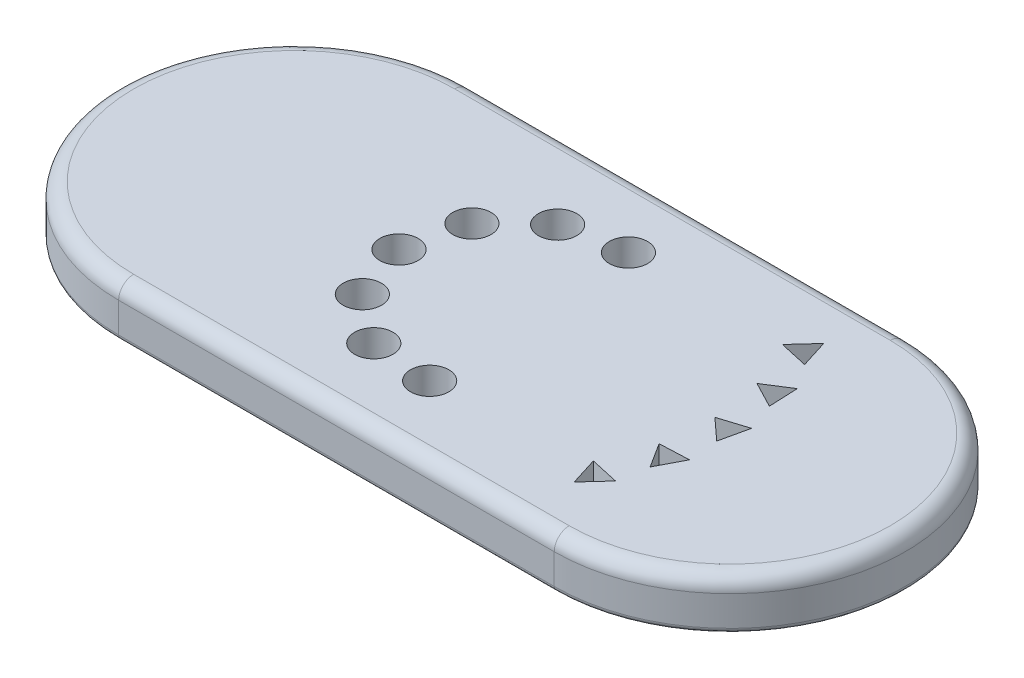
SolidWorks part; units mm, degrees
ref_plane "Front Plane" through (0, 0, 0) normal (0, 0, 1) x (1, 0, 0)
ref_plane "Top Plane" through (0, 0, 0) normal (0, 1, 0) x (1, 0, 0)
ref_plane "Right Plane" through (0, 0, 0) normal (1, 0, 0) x (0, 0, -1)
sketch "Sketch1" plane through (0, 0, 0) normal (0, 1, 0) x (1, 0, 0)
  line L0 (-45.6671, 0) -> (41.3651, 0) construction
  line L1 (-45.6671, 35.0776) -> (41.3651, 35.0776)
  line L2 (-45.6671, -35.0776) -> (41.3651, -35.0776)
  arc A0 (-45.6671, 35.0776) -> (-45.6671, -35.0776) centre (-45.6671, 0) ccw
  arc A1 (41.3651, -35.0776) -> (41.3651, 35.0776) centre (41.3651, 0) ccw
  point P3 (-2.151, 0)
extrude "Boss-Extrude1" add sketch "Sketch1" along normal blind 10
sketch "Sketch2" plane through (0, 10, 0) normal (0, 1, 0) x (1, 0, 0)
  line L0 (-92.1345, 0) -> (94.6589, 0) construction
  line L1 (0, 44.2678) -> (0, -47.9912) construction
  circle A0 centre (0, 21.1148) radius 3.8297
extrude "Cut-Extrude1" cut sketch "Sketch2" against normal blind 10
pattern_circular "CirPattern1" count 7 every 33 about axis through (-2.161, 0, 0.098) along (0, 1, 0) of "Cut-Extrude1"
sketch "Sketch3" plane through (0, 10, 0) normal (0, 1, 0) x (1, 0, 0)
  line L1 (36.9926, 19.3265) -> (35.2397, 24.8894)
  line L2 (35.2397, 24.8894) -> (31.2985, 20.59)
  line L3 (31.2985, 20.59) -> (36.9926, 19.3265)
  circle A0 centre (34.5103, 21.602) radius 1.6837 construction
  point P1 (36.9926, 19.3265)
extrude "Cut-Extrude2" cut sketch "Sketch3" against normal blind 10
pattern_circular "CirPattern2" count 5 every 15 about axis through (-1.8831, 0, 0.0118) along (0, 1, 0) of "Cut-Extrude2"
fillet "Fillet1" radius 3 4 edges at (-80.7448, 10, 0) (-2.151, 10, -35.0776) (76.4428, 10, 0) (-2.151, 10, 35.0776)
fillet "Fillet2" radius 1 4 edges at (-80.7448, 0, 0) (-2.151, 0, -35.0776) (76.4428, 0, 0) (-2.151, 0, 35.0776)
